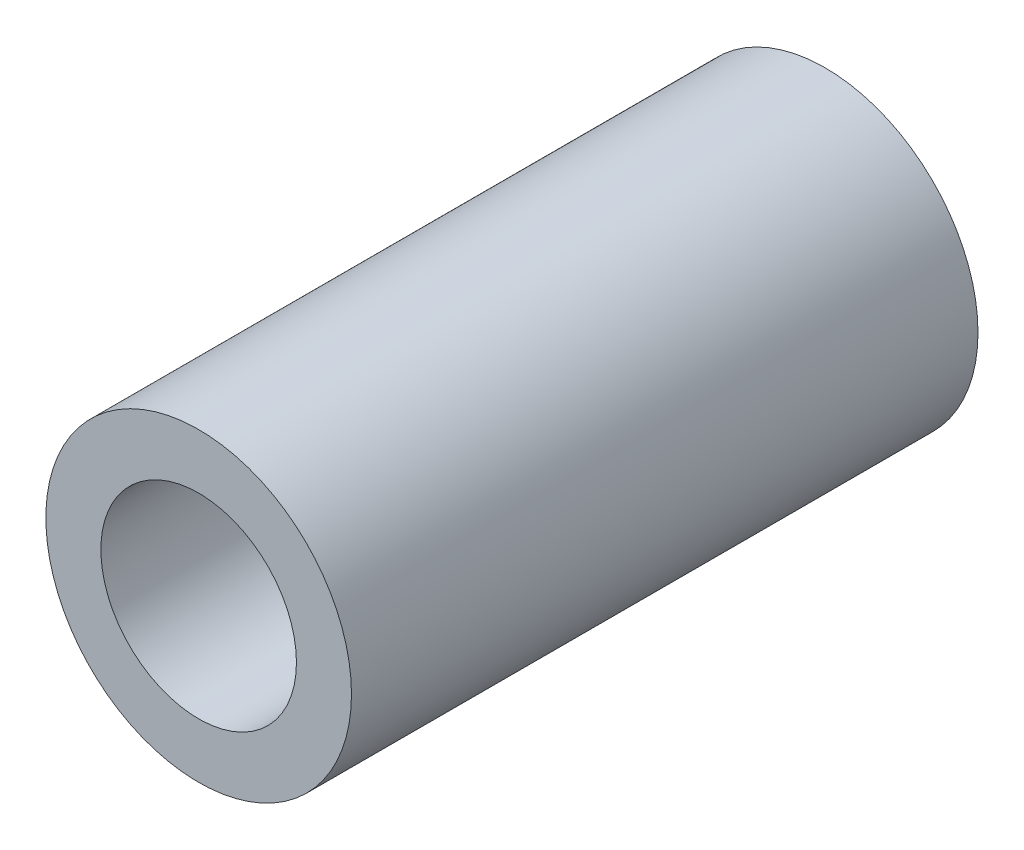
SolidWorks part; units mm, degrees
ref_plane "前视基准面" through (0, 0, 0) normal (0, 0, 1) x (1, 0, 0)
ref_plane "上视基准面" through (0, 0, 0) normal (0, 1, 0) x (1, 0, 0)
ref_plane "右视基准面" through (0, 0, 0) normal (1, 0, 0) x (0, 0, -1)
other "Configuration Table"
sketch "草图1" plane through (0, 0, 0) normal (0, 0, 1) x (1, 0, 0)
  circle A0 centre (0, 0) radius 3.2
  circle A1 centre (0, 0) radius 5
  dimension "D1" = 6.4
  dimension "D2" = 10
extrude "凸台-拉伸1" add sketch "草图1" along normal blind 20.5
